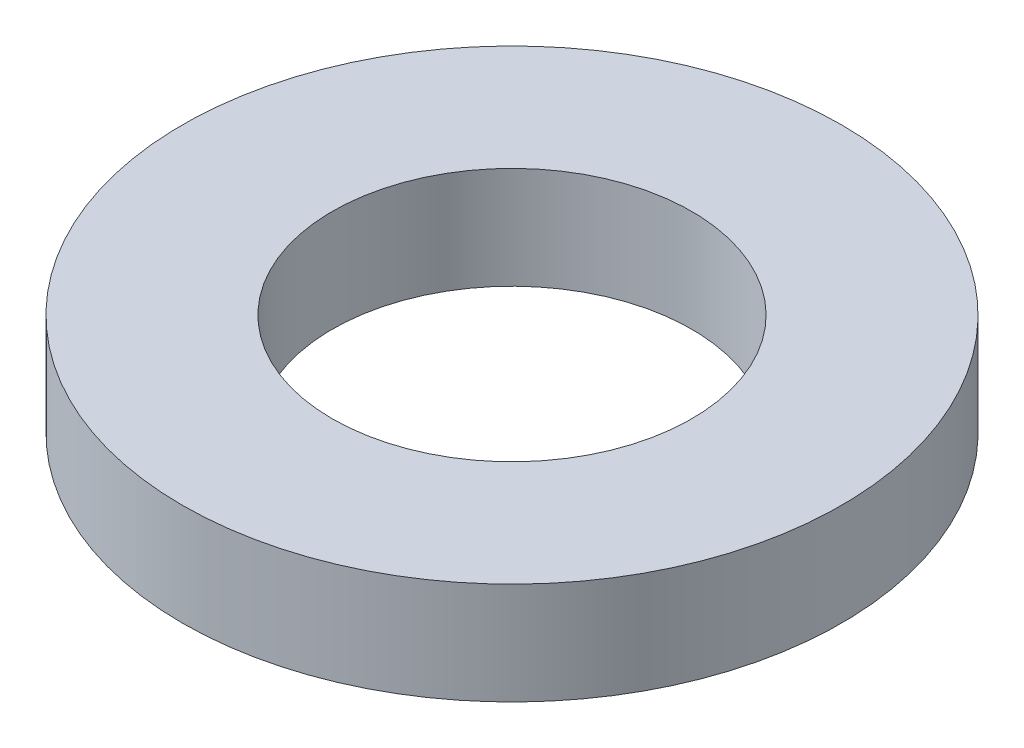
SolidWorks part; units mm, degrees
ref_plane "Front Plane" through (0, 0, 0) normal (0, 0, 1) x (1, 0, 0)
ref_plane "Top Plane" through (0, 0, 0) normal (0, 1, 0) x (1, 0, 0)
ref_plane "Right Plane" through (0, 0, 0) normal (1, 0, 0) x (0, 0, -1)
other "Bounding Box"
ref_plane "Default Plane" through (13.8565, 3.175, 6.7999) normal (0, -1, 0) x (-1, 0, 0)
sketch "Sketch1" plane through (0, 0, 0) normal (0, 1, 0) x (1, 0, 0)
  circle A0 centre (0, 0) radius 6.35
  circle A1 centre (0, 0) radius 11.6459
  dimension "D1" = 12.7
  dimension "D2" = 23.2918
extrude "Boss-Extrude1" add sketch "Sketch1" along normal mid plane 3.6068
